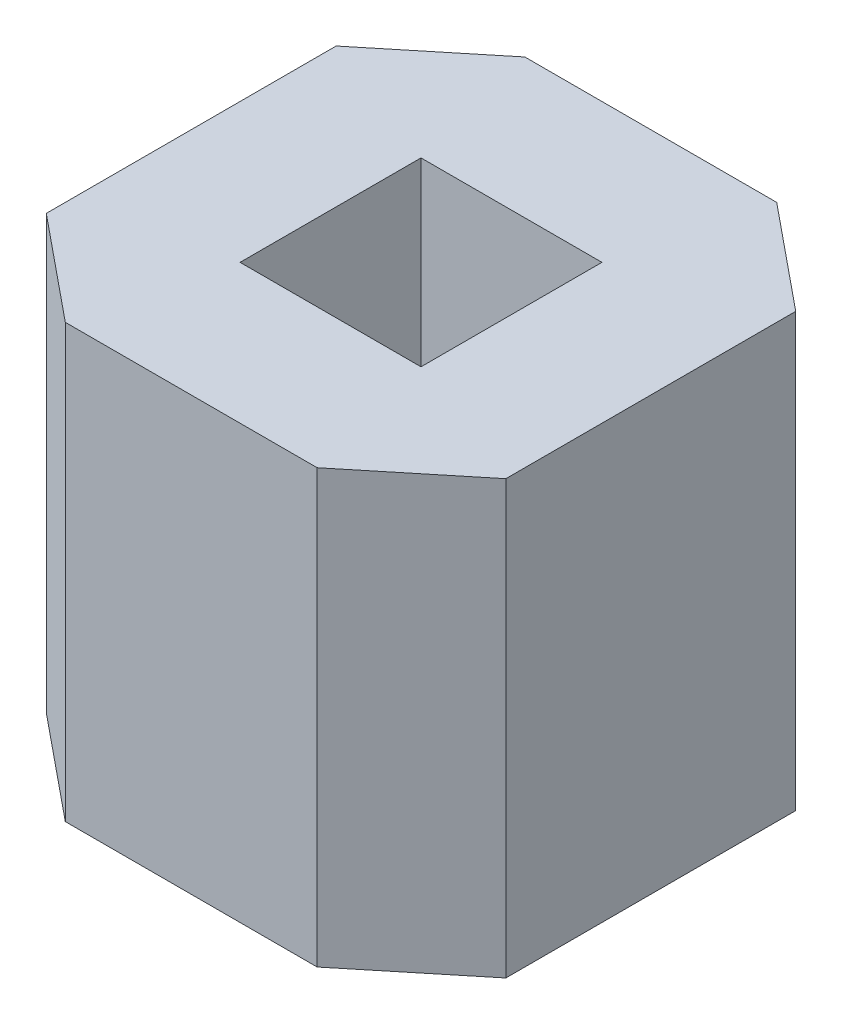
SolidWorks part; units mm, degrees
material "ABS"
ref_plane "Front Plane" through (0, 0, 0) normal (0, 0, 1) x (1, 0, 0)
ref_plane "Top Plane" through (0, 0, 0) normal (0, 1, 0) x (1, 0, 0)
ref_plane "Right Plane" through (0, 0, 0) normal (1, 0, 0) x (0, 0, -1)
sketch "Sketch1" plane through (0, 0, 0) normal (0, 1, 0) x (1, 0, 0)
  line L0 (-39.7929, 5.1937) -> (-37.2529, 5.1937) construction
  line L1 (-39.2189, 3.9237) -> (-37.827, 3.9237)
  line L2 (-39.2189, 6.4637) -> (-37.827, 6.4637)
  line L3 (-39.7929, 4.3926) -> (-39.7929, 5.9948)
  line L4 (-37.2529, 4.3926) -> (-37.2529, 5.9948)
  line L5 (-38.5229, 6.4637) -> (-38.5229, 3.9237) construction
  line L6 (-37.827, 3.9237) -> (-37.2529, 4.3926)
  line L7 (-37.827, 6.4637) -> (-37.2529, 5.9948)
  line L8 (-39.2189, 6.4637) -> (-39.7929, 5.9948)
  line L9 (-39.2189, 3.9237) -> (-39.7929, 4.3926)
  line L10 (-39.0229, 4.6937) -> (-38.0229, 4.6937)
  line L11 (-39.0229, 4.6937) -> (-39.0229, 5.6937)
  line L12 (-38.0229, 4.6937) -> (-38.0229, 5.6937)
  line L13 (-39.0229, 5.6937) -> (-38.0229, 5.6937)
  line L14 (-39.0229, 4.6937) -> (-38.0229, 5.6937) construction
  line L15 (-38.0229, 4.6937) -> (-39.0229, 5.6937) construction
  point P1 (-38.5229, 5.1937)
  dimension "D1" = 2.54
  dimension "D2" = 2.54
  dimension "D3" = 1
extrude "Boss-Extrude2" add sketch "Sketch1" along normal blind 2.39
